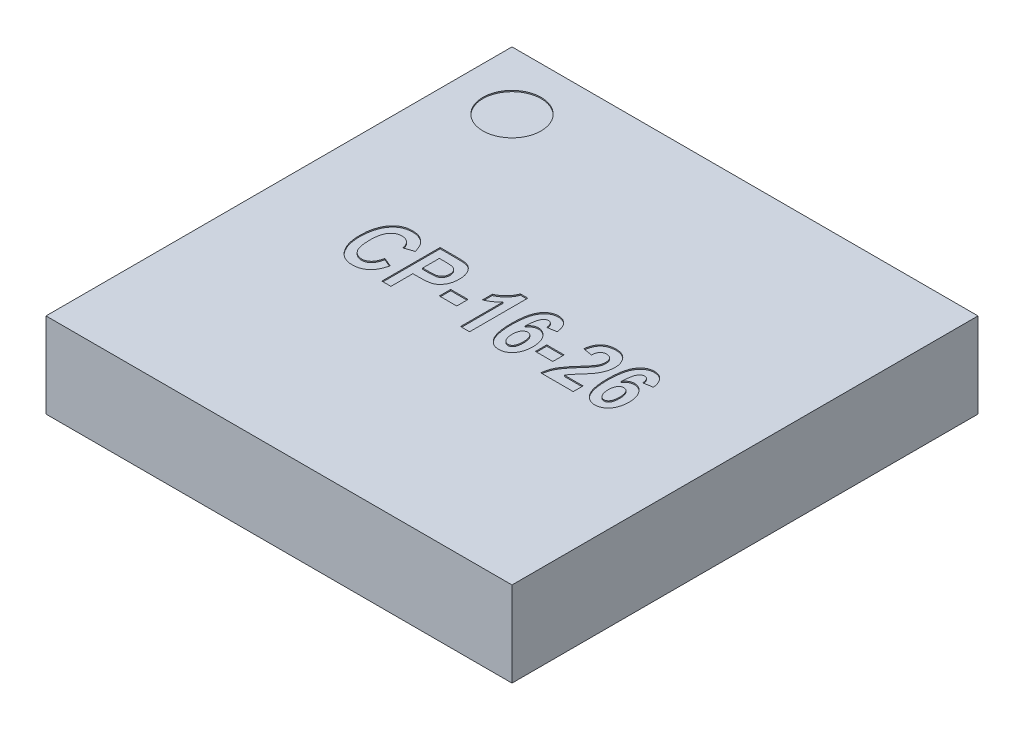
SolidWorks part; units mm, degrees
ref_plane "Front Plane" through (0, 0, 0) normal (0, 0, 1) x (1, 0, 0)
ref_plane "Top Plane" through (0, 0, 0) normal (0, 1, 0) x (1, 0, 0)
ref_plane "Right Plane" through (0, 0, 0) normal (1, 0, 0) x (0, 0, -1)
sketch "Sketch1" plane through (0, 0, 0) normal (0, 1, 0) x (1, 0, 0)
  line L1 (-2, -2) -> (2, -2)
  line L2 (-2, -2) -> (-2, 2)
  line L3 (-2, 2) -> (2, 2)
  line L4 (2, -2) -> (2, 2)
  line L5 (-2, -2) -> (2, 2) construction
  line L6 (-2, 2) -> (2, -2) construction
  point P0 (0, 0)
  dimension "D1" = 4
extrude "Boss-Extrude1" add sketch "Sketch1" along normal blind 0.73
sketch "Sketch2" plane through (0, 0.73, 0) normal (0, 1, 0) x (1, 0, 0)
  line L0 (-2, 2) -> (-2, -2) construction
  line L1 (2, 2) -> (-2, 2) construction
  circle A0 centre (-1.5, 1.5) radius 0.25
  dimension "D1" = 0.5
  dimension "D2" = 0.5
  dimension "D3" = 0.5
extrude "Cut-Extrude1" cut sketch "Sketch2" against normal blind 0.01
sketch "Sketch3" plane through (0, 0.73, 0) normal (0, 1, 0) x (1, 0, 0)
  line L0 (-1.2783, -0.3) -> (1.2783, -0.3) construction
  line L1 (0, -0.4015) -> (0, 0.4015) construction
  line L2 (-0.4015, 0) -> (0.4015, 0) construction
  text T0 "<b>CP-16-26</b>" font "Arial Narrow" height 0.5
  point P2 (0, -0.3)
  point P8 (1.2783, -0.3)
  dimension "D1" = 0.3
extrude "Cut-Extrude2" cut sketch "Sketch3" against normal blind 0.01
